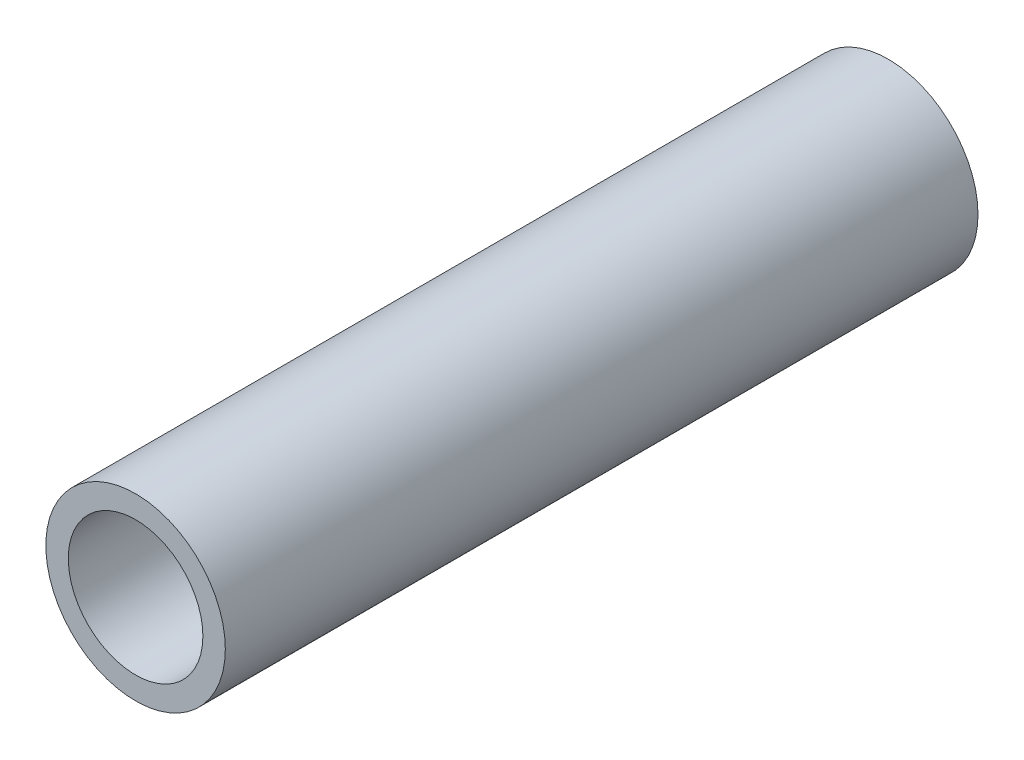
SolidWorks part; units mm, degrees
ref_plane "Front Plane" through (0, 0, 0) normal (0, 0, 1) x (1, 0, 0)
ref_plane "Top Plane" through (0, 0, 0) normal (0, 1, 0) x (1, 0, 0)
ref_plane "Right Plane" through (0, 0, 0) normal (1, 0, 0) x (0, 0, -1)
sketch "Sketch1" plane through (0, 0, 0) normal (0, 0, 1) x (1, 0, 0)
  circle A0 centre (0, 0) radius 3
  circle A1 centre (0, 0) radius 4
  dimension "D1" = 6
  dimension "D2" = 1
extrude "Boss-Extrude1" add sketch "Sketch1" along normal blind 33.55
